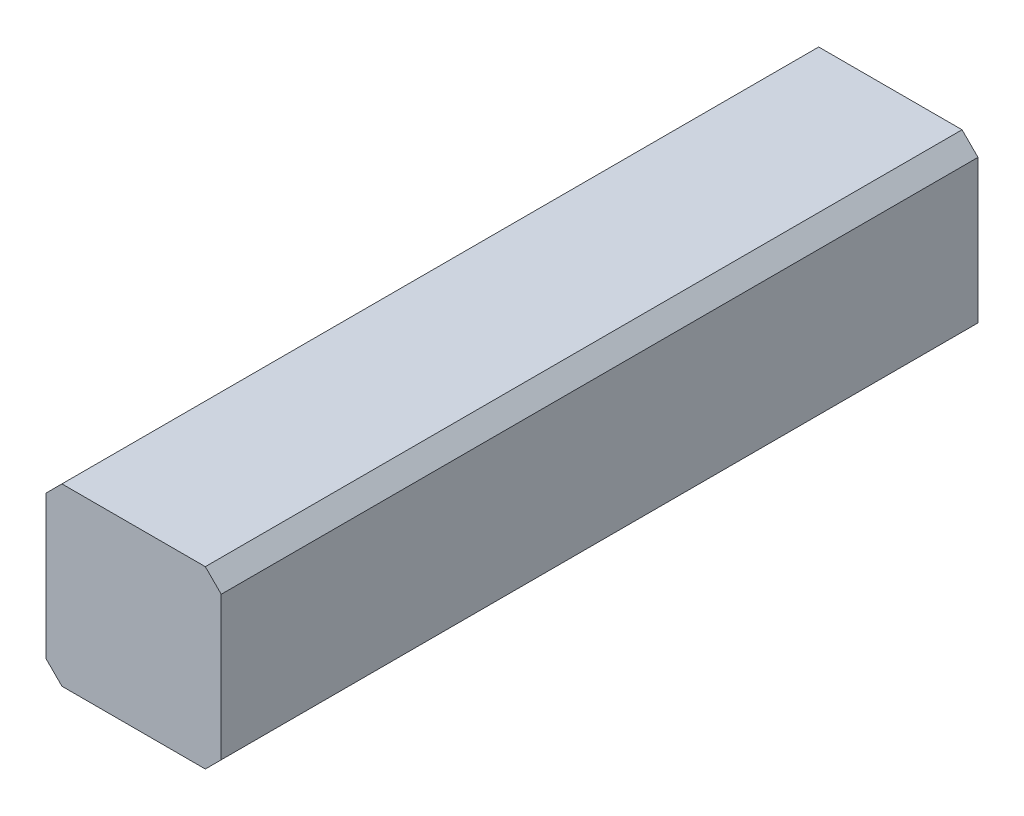
SolidWorks part; units mm, degrees
ref_plane "Plan de face" through (0, 0, 0) normal (0, 0, 1) x (1, 0, 0)
ref_plane "Plan de dessus" through (0, 0, 0) normal (0, 1, 0) x (1, 0, 0)
ref_plane "Plan de droite" through (0, 0, 0) normal (1, 0, 0) x (0, 0, -1)
sketch "Esquisse1" plane through (0, 0, 0) normal (0, 0, 1) x (1, 0, 0)
  line L0 (-11, 9) -> (-9, 11)
  line L1 (-9, 11) -> (9, 11)
  line L2 (-11, 9) -> (-11, -9)
  line L3 (-9, -11) -> (9, -11)
  line L4 (11, 9) -> (11, -9)
  line L5 (-11, 11) -> (11, -11) construction
  line L6 (-11, -11) -> (11, 11) construction
  line L7 (9, 11) -> (11, 9)
  line L8 (9, -11) -> (11, -9)
  line L9 (-11, -9) -> (-9, -11)
  point P0 (0, 0)
  dimension "D1" = 22
  dimension "D2" = 22
extrude "Boss.-Extru.1" add sketch "Esquisse1" along normal blind 95
